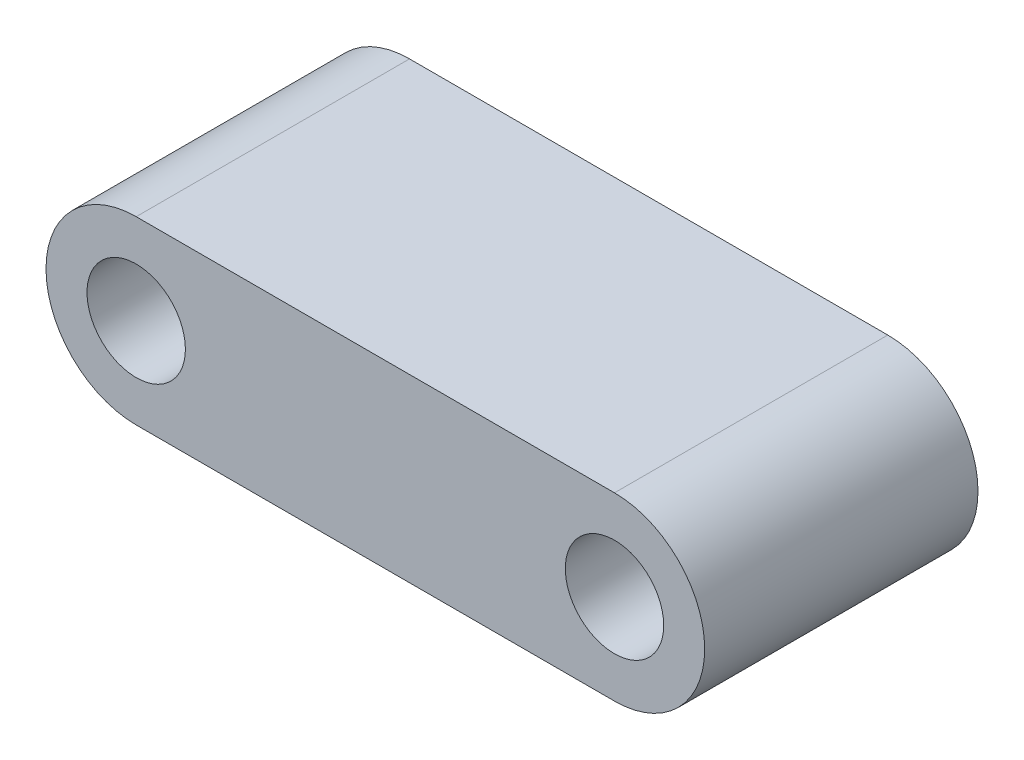
SolidWorks part; units mm, degrees
ref_plane "Alzado" through (0, 0, 0) normal (0, 0, 1) x (1, 0, 0)
ref_plane "Planta" through (0, 0, 0) normal (0, 1, 0) x (1, 0, 0)
ref_plane "Vista lateral" through (0, 0, 0) normal (1, 0, 0) x (0, 0, -1)
sketch "Croquis1" plane through (0, 0, 0) normal (0, 0, 1) x (1, 0, 0)
  line L0 (-7.6, 0) -> (9.9, 0) construction
  line L1 (-7.6, 3.3) -> (9.9, 3.3)
  line L2 (-7.6, -3.3) -> (9.9, -3.3)
  arc A0 (-7.6, 3.3) -> (-7.6, -3.3) centre (-7.6, 0) ccw
  arc A1 (9.9, -3.3) -> (9.9, 3.3) centre (9.9, 0) ccw
  point P2 (1.15, 0)
  dimension "D1" = 17.5
  dimension "D2" = 6.6
extrude "Saliente-Extruir1" add sketch "Croquis1" along normal blind 10
sketch "Croquis7" plane through (0, 0, 10) normal (0, 0, 1) x (1, 0, 0)
  line L0 (-7.6, 3.3) -> (-7.6, -3.3)
  line L1 (9.9, 3.3) -> (9.9, -3.3)
  line L2 (-7.6, -3.3) -> (9.9, -3.3) construction
  line L3 (9.9, 0) -> (-7.6, 0)
  arc A0 (9.9, -3.3) -> (9.9, 3.3) centre (9.9, 0) ccw construction
hole_wizard "Taladro de margen para M31" positions "Croquis8" profile "Croquis9" hole size "M3" standard "Ansi Metric" end condition through all
sketch "Croquis8" plane through (0, 0, 10) normal (0, 0, 1) x (1, 0, 0)
  point P0 (-7.6, 0)
  point P3 (9.9, 0)
sketch "Croquis9" plane through (-7.6, 0, 10) normal (1, 0, 0) x (0, -1, 0)
  line L0 (0, 0) -> (0, 10)
  line L1 (0, 10) -> (1.8, 10)
  line L2 (1.8, 10) -> (1.8, 0)
  line L5 (1.8, 0) -> (0, 0)
  line L11 (0, -6.35) -> (0, 107.95) construction
  dimension "Diámetro de taladro hasta el siguiente" = 3.6
  dimension "Profundidad de taladro hasta el siguiente" = 10
